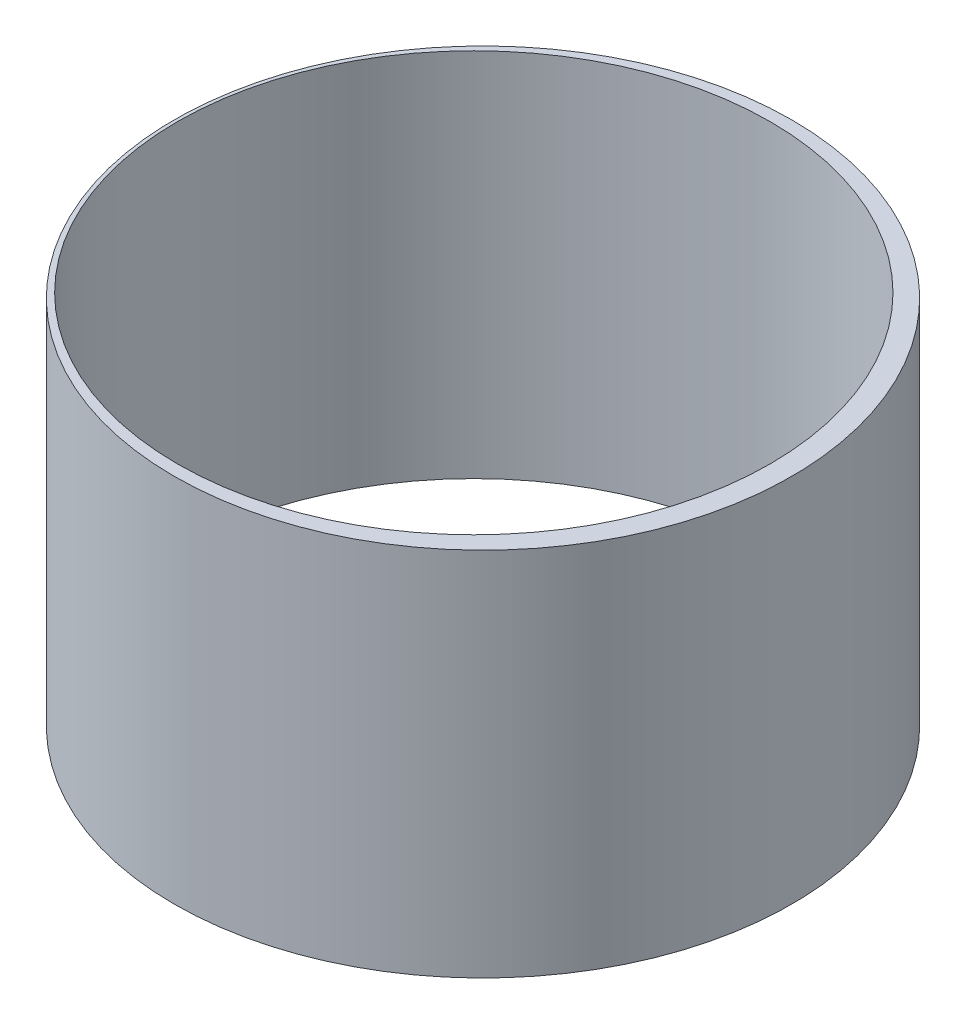
SolidWorks part; units mm, degrees
material "Thornel Mat VMA"
ref_plane "前视基准面" through (0, 0, 0) normal (0, 0, 1) x (1, 0, 0)
ref_plane "上视基准面" through (0, 0, 0) normal (0, 1, 0) x (1, 0, 0)
ref_plane "右视基准面" through (0, 0, 0) normal (1, 0, 0) x (0, 0, -1)
sketch "草图1" plane through (0, 0, 0) normal (0, 1, 0) x (1, 0, 0)
  circle A0 centre (0, 0) radius 25
  circle A1 centre (-0.7446, 0) radius 24
  dimension "D1" = 50
  dimension "D2" = 48
extrude "凸台-拉伸1" add sketch "草图1" along normal blind 30
